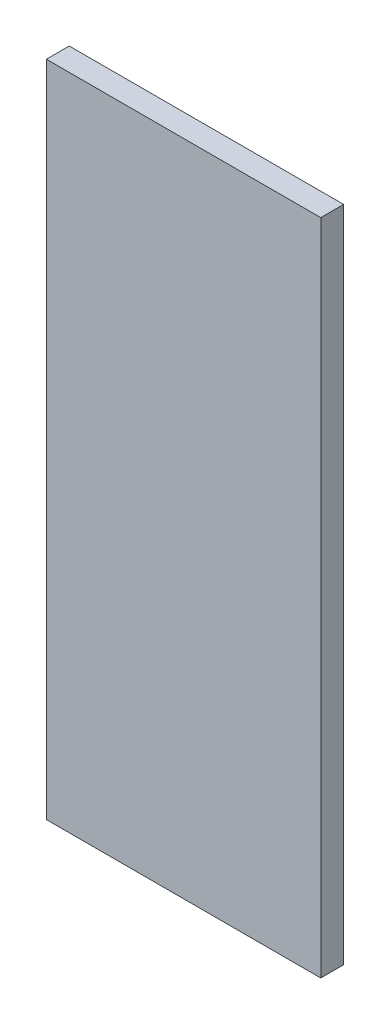
SolidWorks part; units mm, degrees
ref_plane "Front Plane" through (0, 0, 0) normal (0, 0, 1) x (1, 0, 0)
ref_plane "Top Plane" through (0, 0, 0) normal (0, 1, 0) x (1, 0, 0)
ref_plane "Right Plane" through (0, 0, 0) normal (1, 0, 0) x (0, 0, -1)
sketch "Sketch2" plane through (0, 0, 0) normal (0, 1, 0) x (1, 0, 0)
  line L1 (-39.2634, -23.0345) -> (-77.3634, -23.0345)
  line L2 (-39.2634, -23.0345) -> (-39.2634, -19.8595)
  line L3 (-39.2634, -19.8595) -> (-77.3634, -19.8595)
  line L4 (-77.3634, -23.0345) -> (-77.3634, -19.8595)
  dimension "D1" = 3.175
  dimension "D2" = 38.1
extrude "Boss-Extrude1" add sketch "Sketch2" along normal blind 91.44
